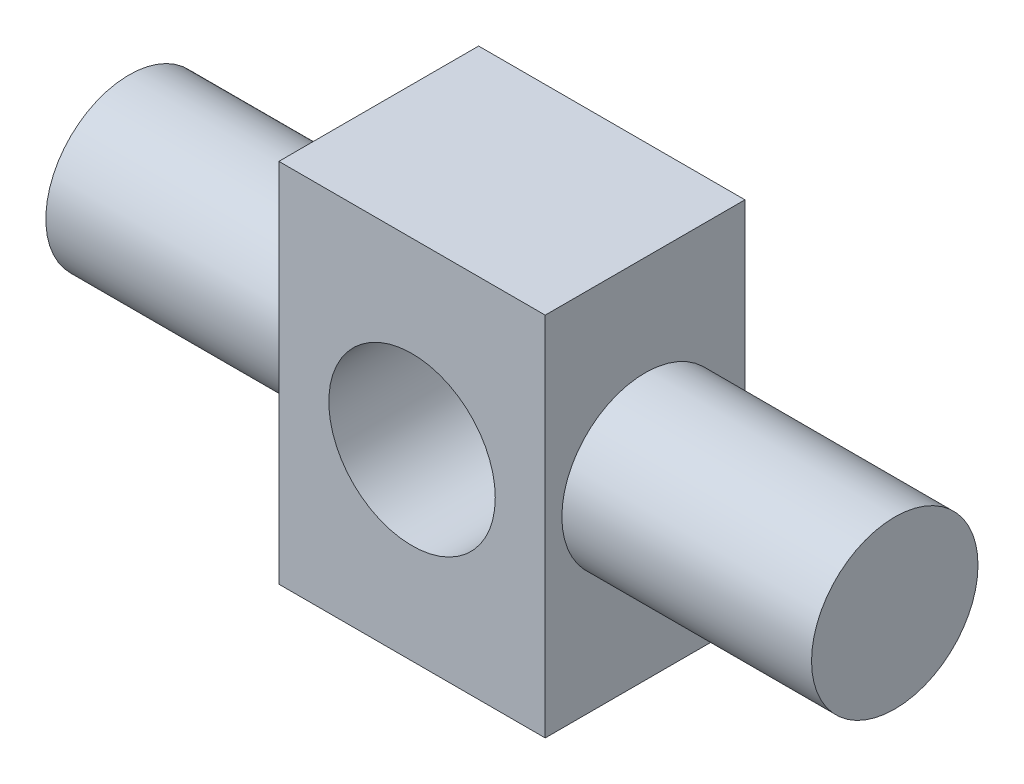
SolidWorks part; units mm, degrees
ref_plane "前视基准面" through (0, 0, 0) normal (0, 0, 1) x (1, 0, 0)
ref_plane "上视基准面" through (0, 0, 0) normal (0, 1, 0) x (1, 0, 0)
ref_plane "右视基准面" through (0, 0, 0) normal (1, 0, 0) x (0, 0, -1)
sketch "草图1" plane through (0, 0, 0) normal (0, 0, 1) x (1, 0, 0)
  line L1 (-8, -11) -> (8, -11)
  line L2 (-8, -11) -> (-8, 11)
  line L3 (-8, 11) -> (8, 11)
  line L4 (8, -11) -> (8, 11)
  line L5 (-8, -11) -> (8, 11) construction
  line L6 (-8, 11) -> (8, -11) construction
  point P0 (0, 0)
  dimension "D1" = 16
  dimension "D2" = 22
extrude "凸台-拉伸1" add sketch "草图1" along normal mid plane 12
sketch "草图2" plane through (8, 0, 0) normal (1, 0, 0) x (0, 0, -1)
  circle A0 centre (0, 0) radius 5
  dimension "D1" = 10
extrude "凸台-拉伸2" add sketch "草图2" along normal blind 15
mirror "镜向1" about plane through (0, 0, 0) normal (1, 0, 0) of "凸台-拉伸2"
sketch "草图3" plane through (0, 0, 6) normal (0, 0, 1) x (1, 0, 0)
  circle A0 centre (0, 0) radius 5
  point P0 (0, 0)
  dimension "D1" = 10
extrude "切除-拉伸1" cut sketch "草图3" against normal through all
